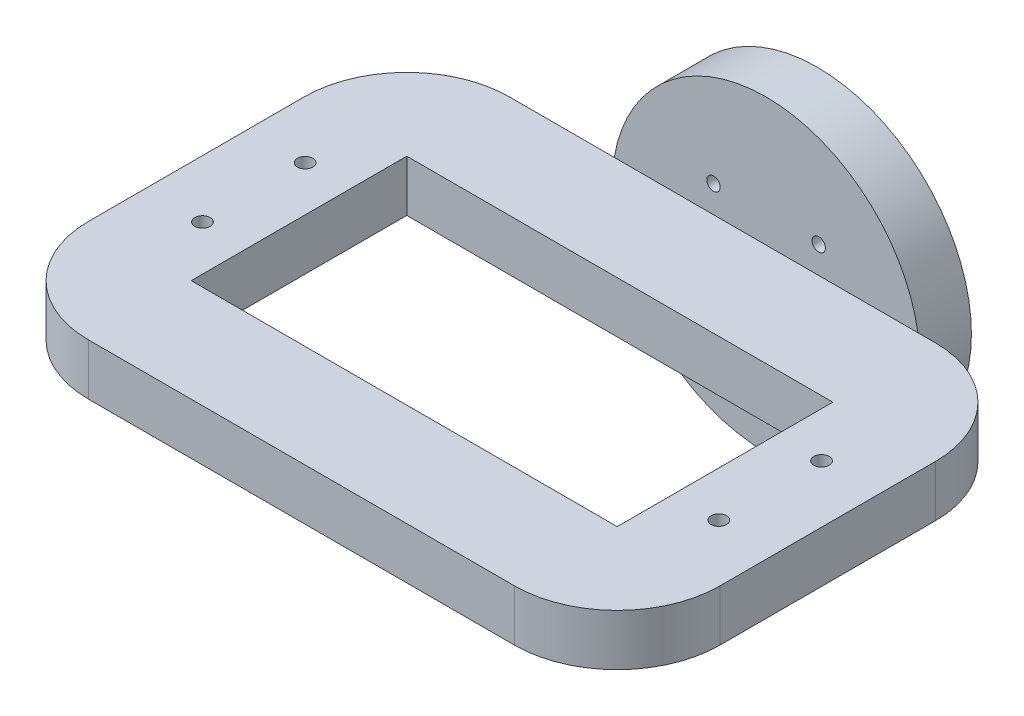
SolidWorks part; units mm, degrees
ref_plane "Front Plane" through (0, 0, 0) normal (0, 0, 1) x (1, 0, 0)
ref_plane "Top Plane" through (0, 0, 0) normal (0, 1, 0) x (1, 0, 0)
ref_plane "Right Plane" through (0, 0, 0) normal (1, 0, 0) x (0, 0, -1)
sketch "Sketch1" plane through (0, 0, 0) normal (0, 0, 1) x (1, 0, 0)
  line L1 (0, 0) -> (-61.5, 0)
  line L2 (0, 0) -> (0, 30)
  line L3 (0, 30) -> (-61.5, 30)
  line L4 (-61.5, 0) -> (-61.5, 30)
  dimension "D1" = 61.5
  dimension "D2" = 30
extrude "Boss-Extrude2" add sketch "Sketch1" along normal blind 5
sketch "Sketch2" plane through (0, 0, 5) normal (0, 0, 1) x (1, 0, 0)
  line L0 (-61.5, 30) -> (-61.5, 0) construction
  line L1 (-61.5, 17.5) -> (0, 17.5)
  line L2 (-61.5, 17.5) -> (-61.5, 12.5)
  line L3 (-61.5, 12.5) -> (0, 12.5)
  line L4 (0, 17.5) -> (0, 12.5)
  line L5 (0, 0) -> (0, 30) construction
  line L6 (0, 30) -> (-61.5, 30) construction
  dimension "D1" = 5
  dimension "D2" = 12.5
extrude "Boss-Extrude3" add sketch "Sketch2" along normal blind 41
sketch "Sketch3" plane through (0, 12.5, 0) normal (0, -1, 0) x (1, 0, 0)
  line L0 (-61.5, 46) -> (-61.5, 5) construction
  line L1 (-51.5, 36) -> (-10, 36)
  line L2 (-51.5, 36) -> (-51.5, 15)
  line L3 (-51.5, 15) -> (-10, 15)
  line L4 (-10, 36) -> (-10, 15)
  line L5 (-61.5, 46) -> (0, 46) construction
  dimension "D1" = 41.5
  dimension "D2" = 21
  dimension "D3" = 10
  dimension "D4" = 10
extrude "Cut-Extrude1" cut sketch "Sketch3" against normal blind 5
sketch "Sketch4" plane through (0, 0, 0) normal (0, 0, -1) x (-1, 0, 0)
  line L0 (0, 30) -> (61.5, 30) construction
  line L1 (61.5, 30) -> (61.5, 0) construction
  circle A0 centre (26.5, 15) radius 15
  dimension "D1" = 30
  dimension "D3" = 35
  dimension "D2" = 15
extrude "Cut-Extrude2" cut sketch "Sketch4" against normal blind 5 flip side to cut
sketch "Sketch5" plane through (0, 0, 0) normal (0, 0, -1) x (-1, 0, 0)
  circle A0 centre (26.5, 15) radius 3.25
extrude "Cut-Extrude5" cut sketch "Sketch5" against normal blind 4
fillet "Fillet1" radius 10 1 edges at (-61.5, 15, 5)
fillet "Fillet2" radius 10 1 edges at (-61.5, 15, 46)
fillet "Fillet3" radius 10 1 edges at (0, 15, 5)
fillet "Fillet4" radius 10 1 edges at (0, 15, 46)
sketch "Sketch7" plane through (0, 12.5, 0) normal (0, -1, 0) x (1, 0, 0)
  circle A0 centre (-55.9, 20.5) radius 0.75
  circle A1 centre (-55.9, 30.5) radius 0.75
  circle A2 centre (-5.6, 30.5) radius 0.75
  circle A3 centre (-5.6, 20.5) radius 0.75
  point P11 (-51.5, 25.5)
  point P16 (-30.75, 15)
  dimension "D1" = 10
  dimension "D2" = 10
  dimension "D3" = 1.5
  dimension "D4" = 1.5
  dimension "D5" = 1.5
  dimension "D6" = 1.5
  dimension "D9" = 50.3
extrude "Cut-Extrude7" cut sketch "Sketch7" against normal blind 5
sketch "Sketch8" plane through (0, 0, 0) normal (0, 0, -1) x (-1, 0, 0)
  circle A0 centre (31.6265, 20.1265) radius 0.65
  circle A1 centre (31.6265, 9.8735) radius 0.65
  circle A2 centre (21.3735, 9.8735) radius 0.65
  circle A3 centre (21.3735, 20.1265) radius 0.65
  dimension "D5" = 1.3
  dimension "D6" = 1.3
  dimension "D7" = 1.3
  dimension "D8" = 1.3
extrude "Cut-Extrude8" cut sketch "Sketch8" against normal blind 5
